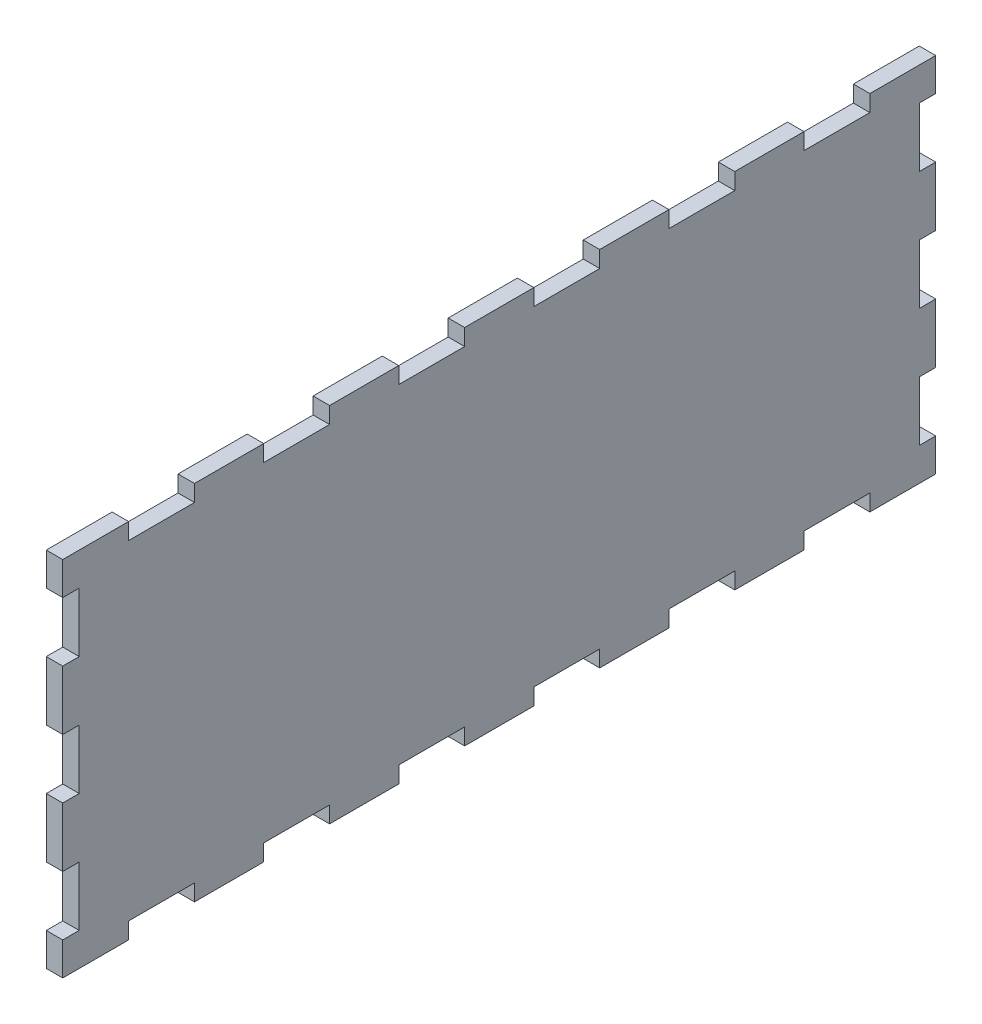
SolidWorks part; units mm, degrees
ref_plane "Front Plane" through (0, 0, 0) normal (0, 0, 1) x (1, 0, 0)
ref_plane "Top Plane" through (0, 0, 0) normal (0, 1, 0) x (1, 0, 0)
ref_plane "Right Plane" through (0, 0, 0) normal (1, 0, 0) x (0, 0, -1)
sketch "Sketch1" plane through (0, 0, 0) normal (1, 0, 0) x (0, 0, -1)
  line L1 (-132.5, 55) -> (132.5, 55)
  line L2 (-132.5, 55) -> (-132.5, -55)
  line L3 (-132.5, -55) -> (132.5, -55)
  line L4 (132.5, 55) -> (132.5, -55)
  line L5 (-132.5, 55) -> (132.5, -55) construction
  line L6 (-132.5, -55) -> (132.5, 55) construction
  point P0 (0, 0)
  dimension "D1" = 265
  dimension "D2" = 110
extrude "Boss-Extrude1" add sketch "Sketch1" along normal blind 5
sketch "Sketch2" plane through (5, 0, 0) normal (1, 0, 0) x (0, 0, -1)
  line L0 (-132.5, 55) -> (-132.5, -55) construction
  line L1 (-127.5, 27) -> (-132.5, 27)
  line L2 (-127.5, 27) -> (-127.5, 45)
  line L3 (-127.5, 45) -> (-132.5, 45)
  line L4 (-132.5, 27) -> (-132.5, 45)
  line L6 (-127.5, 45) -> (-127.5, 55) construction
  line L7 (132.5, 55) -> (-132.5, 55) construction
  line L8 (-127.5, -9) -> (-127.5, 9)
  line L9 (-127.5, -9) -> (-132.5, -9)
  line L10 (-132.5, -9) -> (-132.5, 9)
  line L11 (-127.5, 9) -> (-132.5, 9)
  line L12 (-127.5, -45) -> (-127.5, -27)
  line L13 (-127.5, -45) -> (-132.5, -45)
  line L14 (-132.5, -45) -> (-132.5, -27)
  line L15 (-127.5, -27) -> (-132.5, -27)
  line L16 (-127.5, -45) -> (-127.5, -55) construction
  line L17 (-132.5, -55) -> (132.5, -55) construction
  line L18 (0, 55) -> (0, -55) construction
  line L19 (127.5, -45) -> (132.5, -45)
  line L20 (132.5, -45) -> (132.5, -27)
  line L21 (127.5, -27) -> (132.5, -27)
  line L22 (127.5, -45) -> (127.5, -27)
  line L23 (127.5, -9) -> (132.5, -9)
  line L24 (132.5, -9) -> (132.5, 9)
  line L25 (127.5, 9) -> (132.5, 9)
  line L26 (127.5, -9) -> (127.5, 9)
  line L27 (127.5, 45) -> (132.5, 45)
  line L28 (132.5, 27) -> (132.5, 45)
  line L29 (127.5, 27) -> (132.5, 27)
  line L30 (127.5, 27) -> (127.5, 45)
  line L31 (-132.5, 0) -> (132.5, 0) construction
  line L32 (-71.5, 55) -> (-71.5, 50)
  line L33 (-112.5, 55) -> (-92.5, 55)
  line L34 (-112.5, 55) -> (-112.5, 50)
  line L35 (-112.5, 50) -> (-92.5, 50)
  line L36 (-92.5, 55) -> (-92.5, 50)
  line L37 (-71.5, 55) -> (-51.5, 55)
  line L38 (-51.5, 55) -> (-51.5, 50)
  line L39 (-71.5, 50) -> (-51.5, 50)
  line L40 (-30.5, 55) -> (-30.5, 50)
  line L41 (-30.5, 55) -> (-10.5, 55)
  line L42 (-10.5, 55) -> (-10.5, 50)
  line L43 (-30.5, 50) -> (-10.5, 50)
  line L44 (10.5, 55) -> (10.5, 50)
  line L45 (10.5, 55) -> (30.5, 55)
  line L46 (30.5, 55) -> (30.5, 50)
  line L47 (10.5, 50) -> (30.5, 50)
  line L48 (51.5, 55) -> (51.5, 50)
  line L49 (51.5, 55) -> (71.5, 55)
  line L50 (71.5, 55) -> (71.5, 50)
  line L51 (51.5, 50) -> (71.5, 50)
  line L52 (92.5, 55) -> (92.5, 50)
  line L53 (92.5, 55) -> (112.5, 55)
  line L54 (112.5, 55) -> (112.5, 50)
  line L55 (92.5, 50) -> (112.5, 50)
  line L56 (112.5, 50) -> (132.5, 50) construction
  line L57 (132.5, -55) -> (132.5, 55) construction
  line L58 (-112.5, 50) -> (-132.5, 50) construction
  line L59 (92.5, -55) -> (112.5, -55)
  line L60 (112.5, -55) -> (112.5, -50)
  line L61 (92.5, -50) -> (112.5, -50)
  line L62 (92.5, -55) -> (92.5, -50)
  line L63 (51.5, -55) -> (71.5, -55)
  line L64 (71.5, -55) -> (71.5, -50)
  line L65 (51.5, -50) -> (71.5, -50)
  line L66 (51.5, -55) -> (51.5, -50)
  line L67 (10.5, -55) -> (30.5, -55)
  line L68 (30.5, -55) -> (30.5, -50)
  line L69 (10.5, -50) -> (30.5, -50)
  line L70 (10.5, -55) -> (10.5, -50)
  line L71 (-30.5, -55) -> (-10.5, -55)
  line L72 (-10.5, -55) -> (-10.5, -50)
  line L73 (-30.5, -50) -> (-10.5, -50)
  line L74 (-30.5, -55) -> (-30.5, -50)
  line L75 (-71.5, -55) -> (-51.5, -55)
  line L76 (-51.5, -55) -> (-51.5, -50)
  line L77 (-71.5, -50) -> (-51.5, -50)
  line L78 (-71.5, -55) -> (-71.5, -50)
  line L79 (-112.5, -50) -> (-92.5, -50)
  line L80 (-92.5, -55) -> (-92.5, -50)
  line L81 (-112.5, -55) -> (-92.5, -55)
  line L82 (-112.5, -55) -> (-112.5, -50)
  dimension "D1" = 18
  dimension "D3" = 5
  dimension "D4" = 20
  dimension "D5" = 20
  dimension "D2" = 3
  dimension "D6" = 6
extrude "Cut-Extrude1" cut sketch "Sketch2" against normal blind 5
